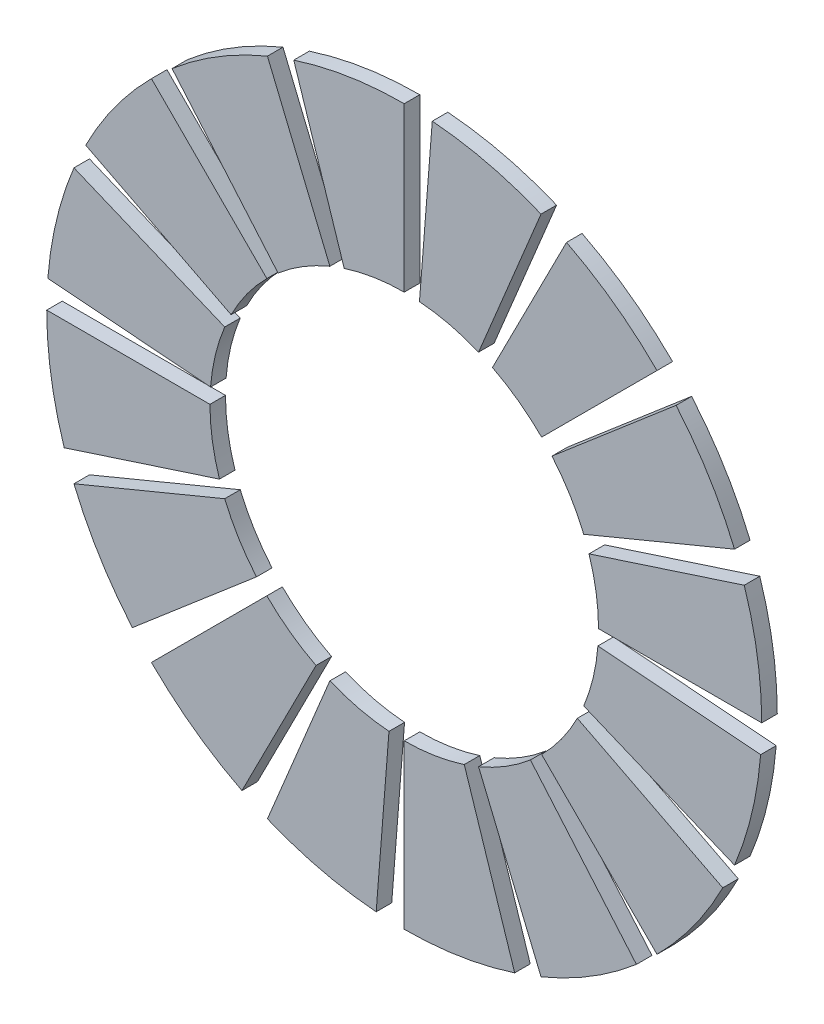
SolidWorks part; units mm, degrees
material "NdFeB"
ref_plane "Ön Düzlem" through (0, 0, 0) normal (0, 0, 1) x (1, 0, 0)
ref_plane "Üst Düzlem" through (0, 0, 0) normal (0, 1, 0) x (1, 0, 0)
ref_plane "Sağ Düzlem" through (0, 0, 0) normal (1, 0, 0) x (0, 0, -1)
sketch "Sketch2" plane through (0, 0, 0) normal (0, 0, 1) x (1, 0, 0)
  line L0 (0, 0) -> (46, 0) construction
  line L1 (0, 0) -> (43.7486, 14.2148) construction
  line L2 (25, 0) -> (46, 0)
  line L3 (23.7764, 7.7254) -> (43.7486, 14.2148)
  circle A0 centre (0, 0) radius 25 construction
  circle A1 centre (0, 0) radius 46 construction
  arc A2 (25, 0) -> (23.7764, 7.7254) centre (0, 0) ccw
  arc A3 (46, 0) -> (43.7486, 14.2148) centre (0, 0) ccw
  point P70 (0, 0)
  dimension "D1" = 50
  dimension "D2" = 92
  dimension "D3" = 18
extrude "Boss-Extrude2" add sketch "Sketch2" along normal blind 2
pattern_circular "CirPattern12" count 16 over 360 about axis through (0, 0, 0) along (0, 0, 1) of bodies 147
